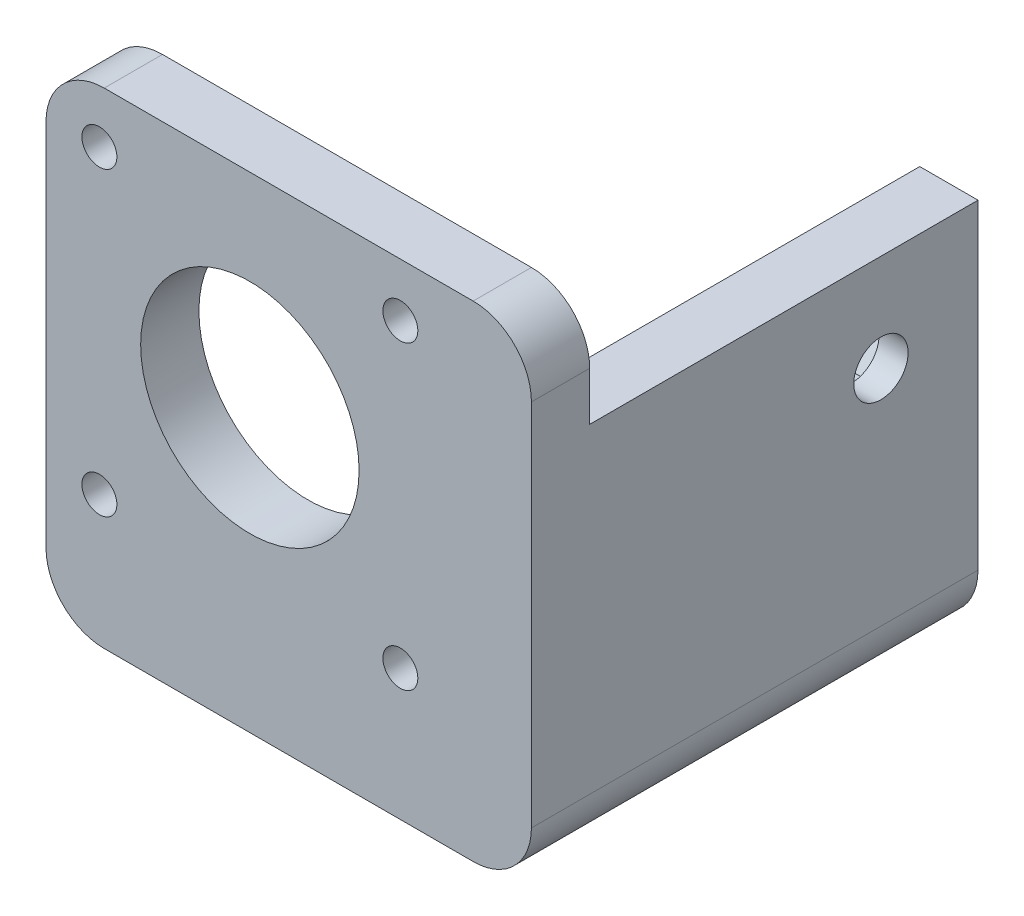
SolidWorks part; units mm, degrees
ref_plane "Front Plane" through (0, 0, 0) normal (0, 0, 1) x (1, 0, 0)
ref_plane "Top Plane" through (0, 0, 0) normal (0, 1, 0) x (1, 0, 0)
ref_plane "Right Plane" through (0, 0, 0) normal (1, 0, 0) x (0, 0, -1)
sketch "Sketch1" plane through (0, 0, 0) normal (0, 0, 1) x (1, 0, 0)
  line L1 (-50, 50) -> (0, 50)
  line L2 (-50, 50) -> (-50, 0)
  line L3 (-50, 0) -> (0, 0)
  line L4 (0, 50) -> (0, 0)
  dimension "D1" = 50
extrude "Boss-Extrude1" add sketch "Sketch1" against normal blind 6
sketch "Sketch2" plane through (0, 0, -6) normal (0, 0, -1) x (-1, 0, 0)
  line L0 (0, 0) -> (0, 50) construction
  line L1 (0, 39) -> (6, 39)
  line L2 (0, 39) -> (0, 0)
  line L3 (0, 0) -> (6, 0)
  line L4 (6, 39) -> (6, 6)
  line L5 (50, 0) -> (0, 0) construction
  line L7 (6, 6) -> (34, 6)
  line L9 (6, 0) -> (34, 0)
  line L10 (34, 6) -> (34, 0)
  dimension "D1" = 39
  dimension "D2" = 6
  dimension "D3" = 28
extrude "Boss-Extrude2" add sketch "Sketch2" along normal blind 40
sketch "Sketch3" plane through (0, 0, 0) normal (0, 0, 1) x (1, 0, 0)
  line L0 (0, 50) -> (-50, 50) construction
  line L1 (-50, 50) -> (-50, 0) construction
  line L2 (-50, 29) -> (0, 29) construction
  line L3 (0, 0) -> (0, 50) construction
  line L4 (-29, 50) -> (-29, 0) construction
  line L5 (-50, 0) -> (0, 0) construction
  point P0 (-44.5, 44.5)
  point P4 (-29, 29)
  point P9 (-13.5, 44.5)
  point P19 (-44.5, 13.5)
  point P20 (-13.5, 13.5)
  dimension "D1" = 5.5
  dimension "D2" = 5.5
  dimension "D3" = 21
  dimension "D4" = 21
hole_wizard "Ø3.6mm Dowel Hole1" positions "Sketch4" profile "Sketch5" hole size "Ø4.0" standard "ANSI Metric" end condition through all
sketch "Sketch4" plane through (0, 0, 0) normal (0, 0, 1) x (1, 0, 0)
  point P0 (-44.5, 44.5)
  point P3 (-13.5, 44.5)
  point P6 (-13.5, 13.5)
  point P9 (-44.5, 13.5)
sketch "Sketch5" plane through (-44.5, 44.5, 0) normal (1, 0, 0) x (0, -1, 0)
  line L0 (0, 0) -> (0, 46)
  line L1 (0, 46) -> (1.8, 46)
  line L2 (1.8, 46) -> (1.8, 0)
  line L5 (1.8, 0) -> (0, 0)
  line L11 (0, -6.35) -> (0, 107.95) construction
  dimension "Thru Hole Dia." = 3.6
  dimension "Thru Hole Depth" = 46
hole_wizard "Ø22.5mm Dowel Hole1" positions "Sketch6" profile "Sketch7" hole size "Ø20.0" standard "ANSI Metric" end condition through all
sketch "Sketch6" plane through (0, 0, 0) normal (0, 0, 1) x (1, 0, 0)
  point P0 (-29, 29)
sketch "Sketch7" plane through (-29, 29, 0) normal (1, 0, 0) x (0, -1, 0)
  line L0 (0, 0) -> (0, 46)
  line L1 (0, 46) -> (11.25, 46)
  line L2 (11.25, 46) -> (11.25, 0)
  line L5 (11.25, 0) -> (0, 0)
  line L11 (0, -6.35) -> (0, 107.95) construction
  dimension "Thru Hole Dia." = 22.5
  dimension "Thru Hole Depth" = 46
hole_wizard "Ø5.6mm Dowel Hole1" positions "3DSketch1" profile "Sketch8" hole size "Ø5.0" standard "ANSI Metric" end condition through all
sketch3d "3DSketch1"
  line L0 (0, 39, -46) -> (0, 39, -6) construction
  line L1 (0, 39, -46) -> (0, 0, -46) construction
  point P0 (0, 29, -36)
  point P7 (0, 0, 0)
  dimension "D1" = 10
  dimension "D2" = 10
sketch "Sketch8" plane through (0, 29, -36) normal (0, 1, 0) x (0, 0, -1)
  line L0 (0, 0) -> (0, 50)
  line L1 (0, 50) -> (2.8, 50)
  line L2 (2.8, 50) -> (2.8, 0)
  line L5 (2.8, 0) -> (0, 0)
  line L11 (0, -6.35) -> (0, 107.95) construction
  dimension "Thru Hole Dia." = 5.6
  dimension "Thru Hole Depth" = 50
hole_wizard "Ø5.6mm Dowel Hole2" positions "Sketch9" profile "Sketch10" hole size "Ø5.0" standard "ANSI Metric" end condition through all
sketch "Sketch9" plane through (0, 0, 0) normal (0, -1, 0) x (-1, 0, 0)
  line L0 (34, 46) -> (34, 6) construction
  line L1 (50, 0) -> (0, 0) construction
  point P0 (24, 15)
  dimension "D1" = 10
  dimension "D2" = 15
sketch "Sketch10" plane through (-24, 0, -15) normal (1, 0, 0) x (0, 0, -1)
  line L0 (0, 0) -> (0, 50)
  line L1 (0, 50) -> (2.8, 50)
  line L2 (2.8, 50) -> (2.8, 0)
  line L5 (2.8, 0) -> (0, 0)
  line L11 (0, -6.35) -> (0, 107.95) construction
  dimension "Thru Hole Dia." = 5.6
  dimension "Thru Hole Depth" = 50
sketch "Sketch12" plane through (0, 6, 0) normal (0, 1, 0) x (1, 0, 0)
  line L1 (-28.2, 12.5751) -> (-24, 10.1503)
  line L2 (-24, 10.1503) -> (-19.8, 12.5751)
  line L3 (-19.8, 12.5751) -> (-19.8, 17.4249)
  line L4 (-19.8, 17.4249) -> (-24, 19.8497)
  line L5 (-24, 19.8497) -> (-28.2, 17.4249)
  line L6 (-28.2, 17.4249) -> (-28.2, 12.5751)
  circle A0 centre (-24, 15) radius 4.2 construction
  dimension "D1" = 8.4
sketch "Sketch13" plane through (-6, 0, 0) normal (-1, 0, 0) x (0, 0, 1)
  line L1 (-40.8497, 29) -> (-38.4249, 24.8)
  line L2 (-38.4249, 24.8) -> (-33.5751, 24.8)
  line L3 (-33.5751, 24.8) -> (-31.1503, 29)
  line L4 (-31.1503, 29) -> (-33.5751, 33.2)
  line L5 (-33.5751, 33.2) -> (-38.4249, 33.2)
  line L6 (-38.4249, 33.2) -> (-40.8497, 29)
  circle A0 centre (-36, 29) radius 4.2 construction
  dimension "D1" = 8.4
extrude "Cut-Extrude1" cut sketch "Sketch12" against normal blind 3
extrude "Cut-Extrude2" cut sketch "Sketch13" against normal blind 3
fillet "Fillet1" radius 6 4 edges at (-50, 0, -3) (-50, 50, -3) (0, 0, -23) (0, 50, -3)
equation "\"D4@Sketch3\"=\"D3@Sketch3\""
equation "\"D2@Sketch3\"=\"D1@Sketch3\""
